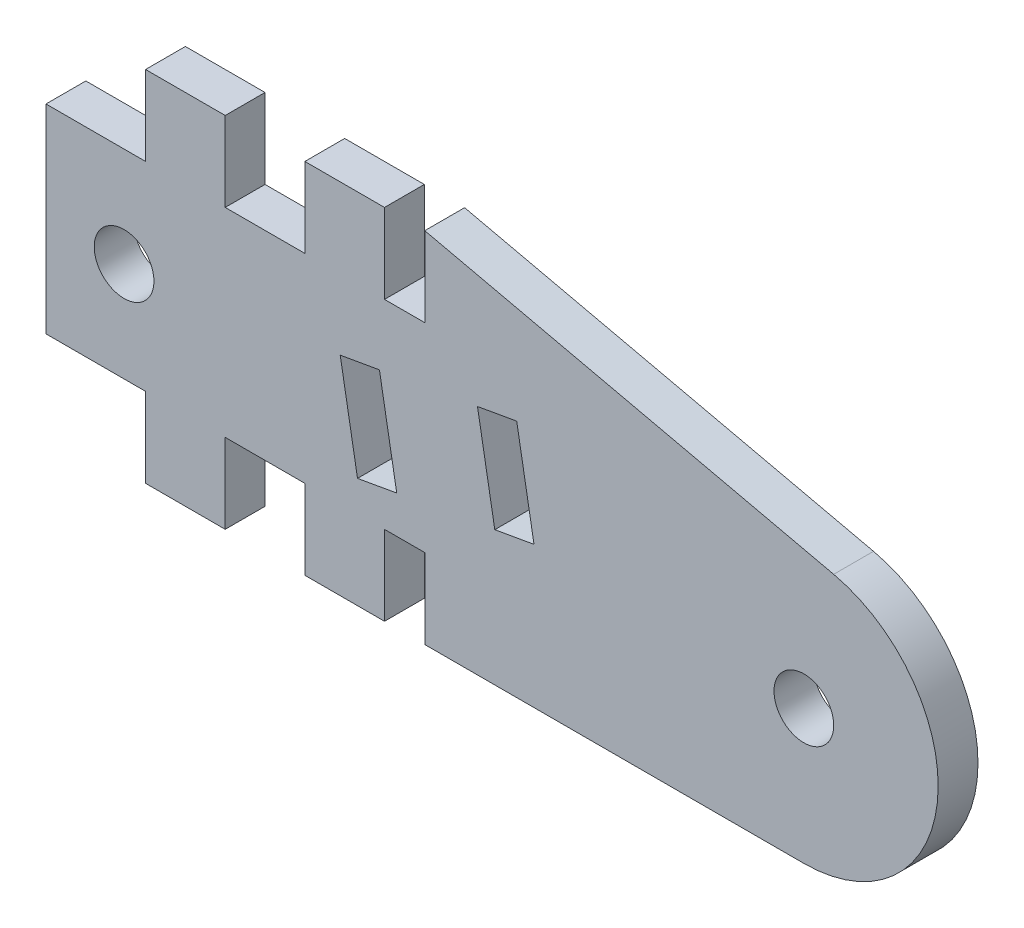
SolidWorks part; units mm, degrees
ref_plane "Front Plane" through (0, 0, 0) normal (0, 0, 1) x (1, 0, 0)
ref_plane "Top Plane" through (0, 0, 0) normal (0, 1, 0) x (1, 0, 0)
ref_plane "Right Plane" through (0, 0, 0) normal (1, 0, 0) x (0, 0, -1)
sketch "Sketch1" plane through (0, 0, 0) normal (0, 0, 1) x (1, 0, 0)
  line L0 (5, 0) -> (9, 0)
  line L1 (5, 4) -> (5, 0)
  line L2 (5, 14) -> (0, 14)
  line L3 (9, 4) -> (13, 4)
  line L4 (13, 4) -> (13, 0)
  line L5 (9, 0) -> (9, 4)
  line L6 (13, 0) -> (17, 0)
  line L7 (17, 0) -> (17, 4)
  line L8 (17, 4) -> (19.0216, 4)
  line L9 (0, 14) -> (0, 4)
  line L10 (19.0216, 4) -> (19.0216, 0)
  line L11 (17, 14) -> (19.0216, 14)
  line L12 (17, 18) -> (17, 14)
  line L13 (13, 18) -> (17, 18)
  line L14 (9, 18) -> (9, 14)
  line L15 (13, 14) -> (13, 18)
  line L16 (9, 14) -> (13, 14)
  line L17 (0, 4) -> (5, 4)
  line L18 (5, 14) -> (5, 18)
  line L19 (5, 18) -> (9, 18)
  line L20 (19.0216, 0) -> (38.0595, 0)
  line L21 (27.99, 0) -> (27.99, -6.4753) construction
  line L22 (19.0216, 14) -> (19.0216, 18)
  line L23 (19.0216, 18) -> (39.5576, 13.3222)
  line L27 (23.6391, 12.0249) -> (21.6695, 11.6776)
  line L32 (16.7455, 10.8093) -> (17.6137, 5.8853)
  line L33 (16.7455, 10.8093) -> (14.7759, 10.462)
  line L34 (14.7759, 10.462) -> (15.6441, 5.538)
  line L35 (15.6441, 5.538) -> (17.6137, 5.8853)
  line L36 (21.6695, 11.6776) -> (22.5378, 6.7535)
  line L37 (22.5378, 6.7535) -> (24.5074, 7.1008)
  line L38 (23.6391, 12.0249) -> (24.5074, 7.1008)
  arc A0 (38.0595, 0) -> (39.5576, 13.3222) centre (38.0595, 6.7453) ccw
  circle A1 centre (3.9205, 9) radius 1.5
  circle A2 centre (38.0595, 6.7453) radius 12.12 construction
  circle A4 centre (38.0595, 6.7453) radius 1.5
  dimension "D1" = 3
  dimension "D2" = 6.7453
  dimension "D7" = 24.24
  dimension "D3" = 3.9205
  dimension "D4" = 14.7759
  dimension "D5" = 15.6441
  dimension "D6" = 16.7455
  dimension "D8" = 21.6695
  dimension "D16" = 9
  dimension "D12" = 5.538
  dimension "D13" = 5.8853
  dimension "ThumbLinkLengthMCP" = 18.99
  dimension "D9" = 9
  dimension "D10" = 18
  dimension "D11" = 19.0216
extrude "Boss-Extrude1" add sketch "Sketch1" along normal blind 2
equation "\"ThumbLinkLengthMCP@Sketch1\"= \"HB@parametersSketch@prostheticParameters.SLDPRT\" * 0.211"
